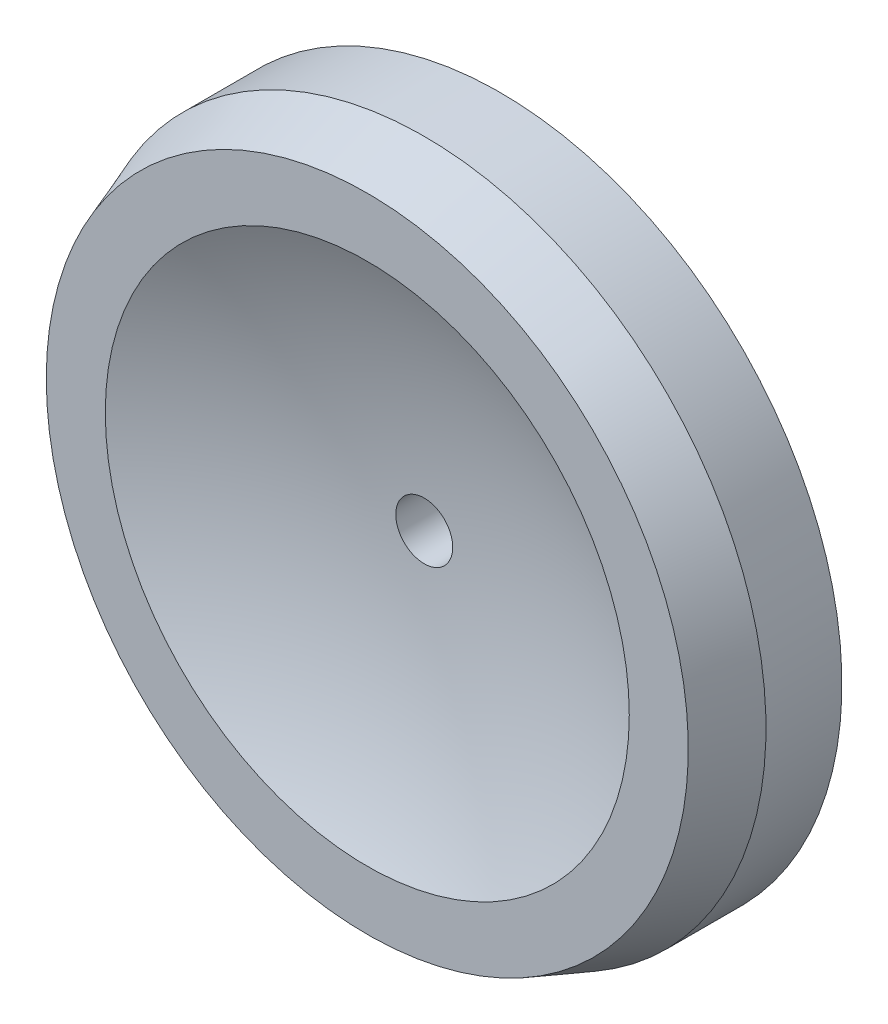
SolidWorks part; units mm, degrees
ref_plane "Alzado" through (0, 0, 0) normal (0, 0, 1) x (1, 0, 0)
ref_plane "Planta" through (0, 0, 0) normal (0, 1, 0) x (1, 0, 0)
ref_plane "Vista lateral" through (0, 0, 0) normal (1, 0, 0) x (0, 0, -1)
ref_plane "Plane1" through (0, -10.646, 0) normal (0, -1, 0) x (1, 0, 0)
sketch "Sketch1" plane through (0, -10.646, 0) normal (0, -1, 0) x (1, 0, 0)
  line L0 (5.597, 1.52) -> (5.5424, 1.67)
  line L1 (5.5424, 1.67) -> (5.387, 1.67)
  line L2 (4.772, 1.52) -> (4.772, 1.32)
  line L3 (4.772, 1.32) -> (5.597, 1.32)
  line L4 (5.597, 1.32) -> (5.597, 1.52)
  line L5 (4.697, 1.67) -> (4.697, 1.32) construction
  arc A0 (5.387, 1.67) -> (4.772, 1.52) centre (4.697, 3.1632) cw
  dimension "D1" = 1.645
  dimension "D2" = 0.075
  dimension "D3" = 0.69
  dimension "D4" = 0.8454
  dimension "D5" = 0.9
  dimension "D6" = 0.2
revolve "Revolve1" add sketch "Sketch1" angle 360 about L5
